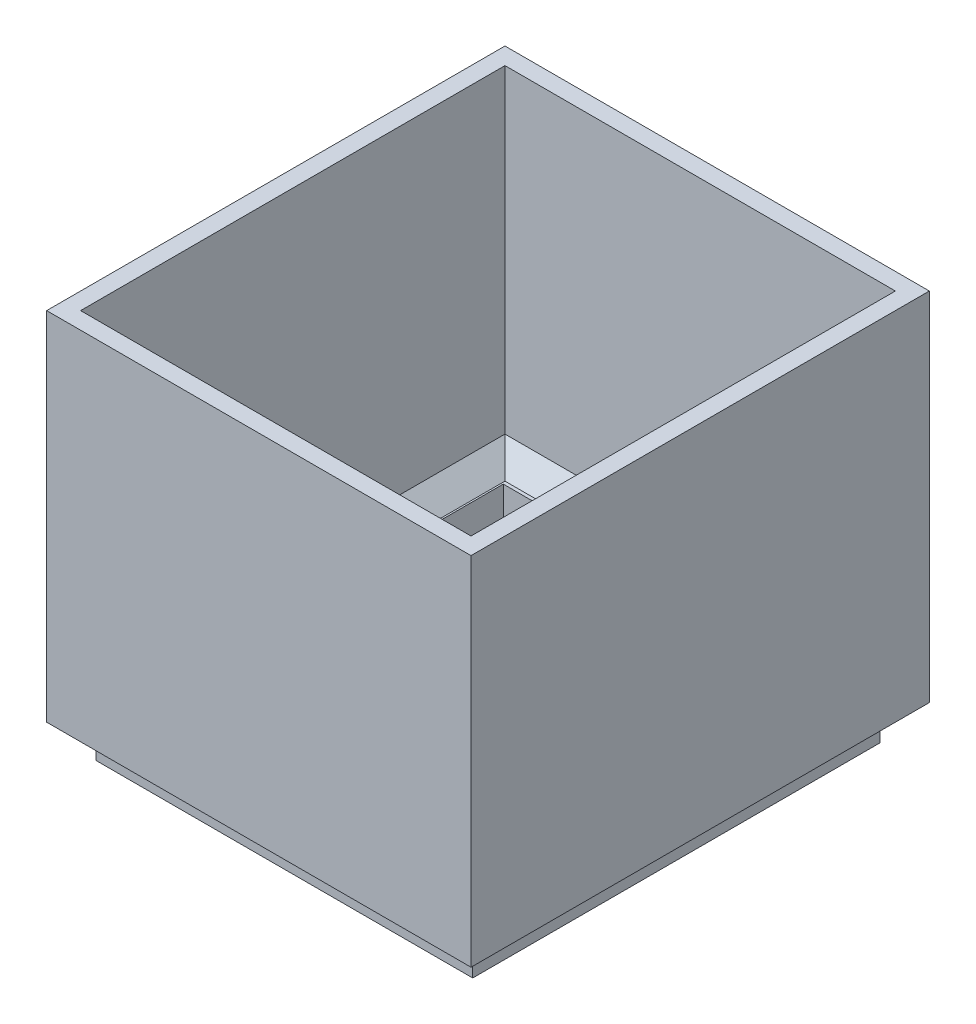
SolidWorks part; units mm, degrees
material "ABS"
ref_plane "Front" through (0, 0, 0) normal (0, 0, 1) x (1, 0, 0)
ref_plane "Top" through (0, 0, 0) normal (0, 1, 0) x (1, 0, 0)
ref_plane "Right" through (0, 0, 0) normal (1, 0, 0) x (0, 0, -1)
sketch "Sketch1" plane through (0, 0, 0) normal (0, 1, 0) x (1, 0, 0)
  line L1 (-51, 55.5) -> (51, 55.5)
  line L2 (-51, 55.5) -> (-51, -55.5)
  line L3 (-51, -55.5) -> (51, -55.5)
  line L4 (51, 55.5) -> (51, -55.5)
  line L5 (-51, 55.5) -> (51, -55.5) construction
  line L6 (-51, -55.5) -> (51, 55.5) construction
  line L7 (-55.5, 60) -> (55.5, 60)
  line L8 (-55.5, 60) -> (-55.5, -60)
  line L9 (-55.5, -60) -> (55.5, -60)
  line L10 (55.5, 60) -> (55.5, -60)
  line L11 (-55.5, 60) -> (55.5, -60) construction
  line L12 (-55.5, -60) -> (55.5, 60) construction
  point P0 (0, 0)
  point P6 (0, 0)
  dimension "D1" = 111
  dimension "D2" = 102
  dimension "D3" = 120
  dimension "D4" = 111
extrude "Boss-Extrude1" add sketch "Sketch1" along normal blind 10
sketch "Sketch2" plane through (0, 10, 0) normal (0, 1, 0) x (1, 0, 0)
  line L5 (-62.5, 67.5) -> (62.5, 67.5)
  line L6 (-62.5, 67.5) -> (-62.5, -67.5)
  line L11 (-62.5, -67.5) -> (62.5, -67.5)
  line L12 (62.5, 67.5) -> (62.5, -67.5)
  line L13 (-62.5, 67.5) -> (62.5, -67.5) construction
  line L14 (-62.5, -67.5) -> (62.5, 67.5) construction
  line L15 (-51, 55.5) -> (51, 55.5)
  line L16 (-51, 55.5) -> (-51, -55.5)
  line L17 (-51, -55.5) -> (51, -55.5)
  line L18 (51, 55.5) -> (51, -55.5)
  line L19 (-51, 55.5) -> (51, -55.5) construction
  line L20 (-51, -55.5) -> (51, 55.5) construction
  point P0 (0, 0)
  point P7 (0, 0)
  dimension "D1" = 125
  dimension "D2" = 135
extrude "Boss-Extrude2" add sketch "Sketch2" along normal blind 5
sketch "Sketch4" plane through (0, 15, 0) normal (0, 1, 0) x (1, 0, 0)
  line L1 (62.5, 67.5) -> (-62.5, 67.5)
  line L2 (62.5, 67.5) -> (62.5, -67.5)
  line L3 (62.5, -67.5) -> (-62.5, -67.5)
  line L4 (-62.5, 67.5) -> (-62.5, -67.5)
  line L5 (62.5, 67.5) -> (-62.5, -67.5) construction
  line L6 (62.5, -67.5) -> (-62.5, 67.5) construction
  line L7 (57.5, 62.5) -> (-57.5, 62.5)
  line L8 (57.5, 62.5) -> (57.5, -62.5)
  line L9 (57.5, -62.5) -> (-57.5, -62.5)
  line L10 (-57.5, 62.5) -> (-57.5, -62.5)
  line L11 (57.5, 62.5) -> (-57.5, -62.5) construction
  line L12 (57.5, -62.5) -> (-57.5, 62.5) construction
  point P0 (0, 0)
  point P7 (0, 0)
  dimension "D1" = 5
  dimension "D2" = 5
extrude "Boss-Extrude4" add sketch "Sketch4" along normal blind 100
chamfer "Chamfer1" distance 6 angle 45 4 edges at (57.5, 15, 0) (0, 15, 62.5) (-57.5, 15, 0) (0, 15, -62.5)
